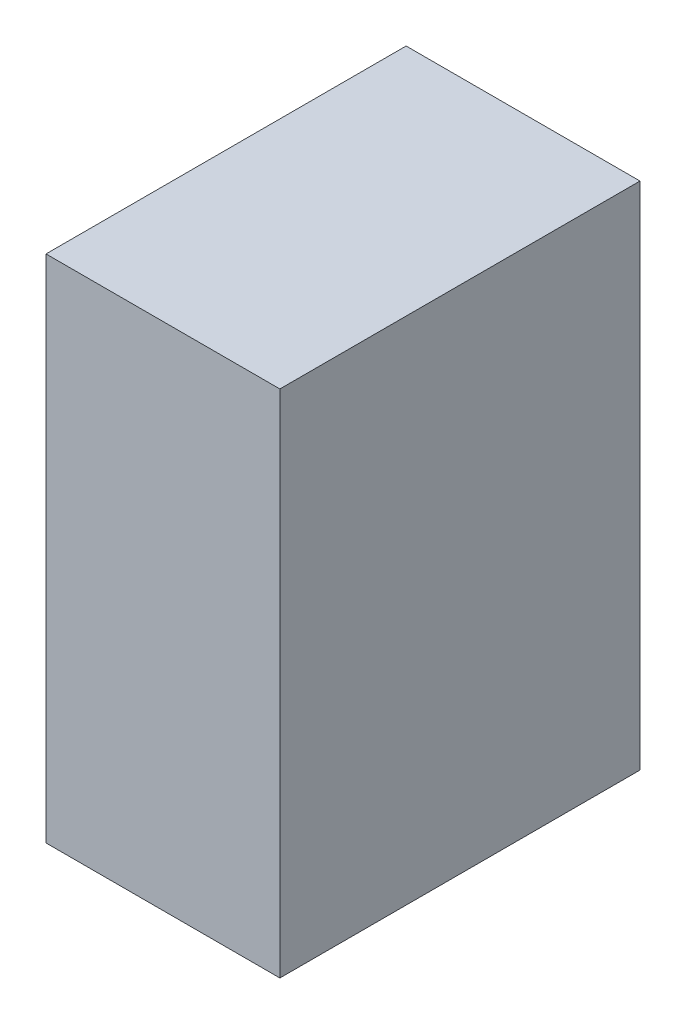
SolidWorks part; units mm, degrees
ref_plane "Front Plane" through (0, 0, 0) normal (0, 0, 1) x (1, 0, 0)
ref_plane "Top Plane" through (0, 0, 0) normal (0, 1, 0) x (1, 0, 0)
ref_plane "Right Plane" through (0, 0, 0) normal (1, 0, 0) x (0, 0, -1)
sketch "Sketch1" plane through (0, 0, 0) normal (0, 1, 0) x (1, 0, 0)
  line L1 (-34.095, -52.5) -> (34.095, -52.5)
  line L2 (-34.095, -52.5) -> (-34.095, 52.5)
  line L3 (-34.095, 52.5) -> (34.095, 52.5)
  line L4 (34.095, -52.5) -> (34.095, 52.5)
  line L5 (-34.095, -52.5) -> (34.095, 52.5) construction
  line L6 (-34.095, 52.5) -> (34.095, -52.5) construction
  point P0 (0, 0)
  dimension "D1" = 68.19
  dimension "D2" = 105
extrude "Boss-Extrude1" add sketch "Sketch1" along normal blind 148.74
